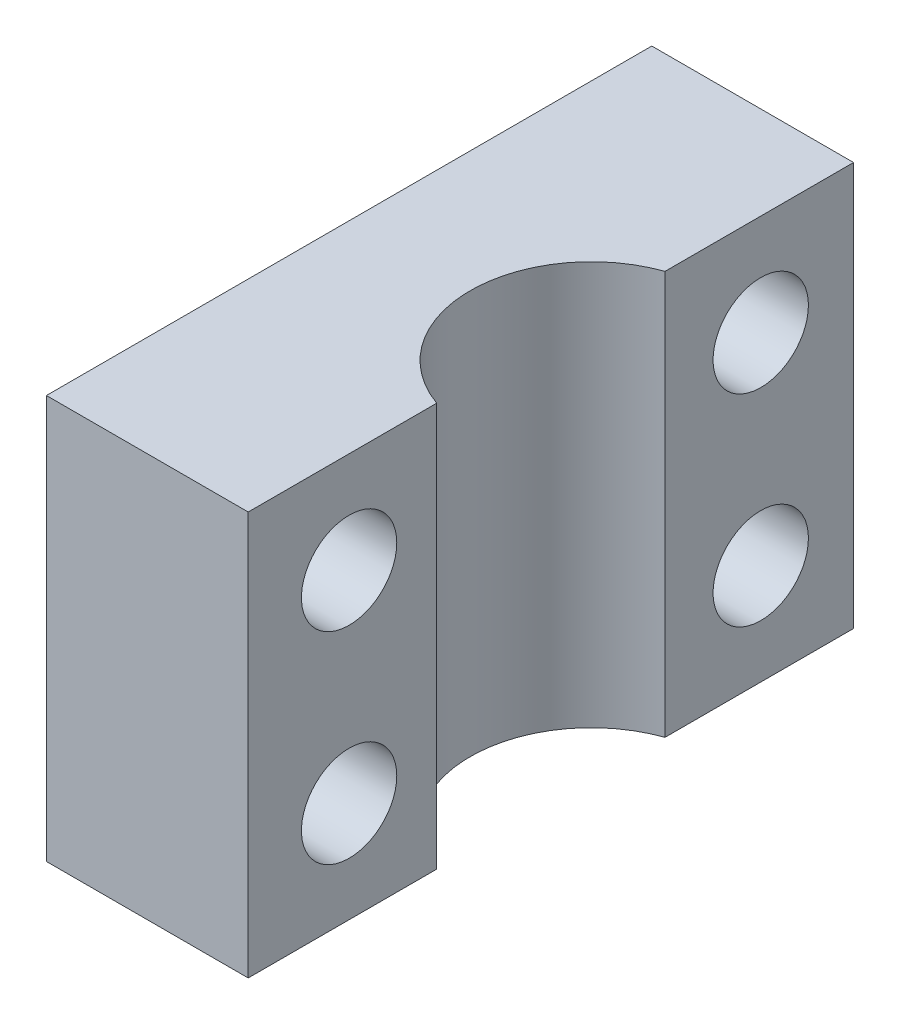
SolidWorks part; units mm, degrees
ref_plane "Front Plane" through (0, 0, 0) normal (0, 0, 1) x (1, 0, 0)
ref_plane "Top Plane" through (0, 0, 0) normal (0, 1, 0) x (1, 0, 0)
ref_plane "Right Plane" through (0, 0, 0) normal (1, 0, 0) x (0, 0, -1)
sketch "Sketch1" plane through (0, 0, 0) normal (0, 1, 0) x (1, 0, 0)
  line L1 (0, 0) -> (12.7, 0)
  line L2 (0, 0) -> (0, 19.05)
  line L3 (0, 19.05) -> (12.7, 19.05)
  line L4 (12.7, 0) -> (12.7, 19.05)
  dimension "D1" = 12.7
  dimension "D2" = 19.05
extrude "Boss-Extrude1" add sketch "Sketch1" along normal blind 12.7
sketch "Sketch4" plane through (0, 12.7, 0) normal (0, 1, 0) x (1, 0, 0)
  line L0 (0, 9.525) -> (6.35, 19.05)
  line L1 (0, 19.05) -> (0, 0) construction
  line L2 (12.7, 19.05) -> (0, 19.05) construction
  line L3 (6.35, 19.05) -> (0, 19.05)
  line L4 (0, 19.05) -> (0, 0)
  line L5 (0, 0) -> (6.35, 0)
  line L6 (0, 0) -> (12.7, 0) construction
  line L7 (6.35, 0) -> (0, 9.525)
  line L8 (12.7, 0) -> (12.7, 19.05) construction
  circle A0 centre (13.97, 9.525) radius 3.81
  point P17 (13.97, 9.525)
  line M1 (0, 19.05) -> (0, 0)
  line M2 (0, 0) -> (12.7, 0)
  line M3 (12.7, 0) -> (12.7, 19.05)
  line M4 (12.7, 19.05) -> (0, 19.05)
  dimension "D1" = 7.62
  dimension "D2" = 1.27
extrude "Cut-Extrude2" cut sketch "Sketch4" against normal blind 12.7 contours L0 M1 M4 | L7 M2 M1 | A0 M3
sketch "Sketch5" plane through (12.7, 0, 0) normal (1, 0, 0) x (0, 0, -1)
  line L0 (0, 12.7) -> (5.9329, 12.7) construction
  line L1 (0, 12.7) -> (0, 0) construction
  circle A0 centre (3.175, 9.525) radius 1.5
  circle A1 centre (16.129, 9.525) radius 1.5
  circle A2 centre (16.129, 3.175) radius 1.5
  circle A3 centre (3.175, 3.175) radius 1.5
  dimension "D1" = 3
  dimension "D2" = 3.175
  dimension "D3" = 3.175
  dimension "D4" = 2
  dimension "D5" = 2
extrude "Cut-Extrude3" cut sketch "Sketch5" against normal blind 12.7
sketch "Sketch6" plane through (0, 0, 0) normal (0, -1, 0) x (1, 0, 0)
  line L0 (6.35, 0) -> (6.35, -5.5703)
  line L2 (2.6365, -5.5703) -> (6.35, 0)
  line L3 (2.6365, -5.5703) -> (6.35, -5.5703)
  line L4 (6.35, 0) -> (0, -9.525) construction
extrude "Cut-Extrude4" cut sketch "Sketch6" against normal blind 12.7
ref_plane "Plane1" through (0, 0, -9.525) normal (0, 0, -1) x (0, 1, 0)
mirror "Mirror1" about plane through (0, 0, -9.525) normal (0, 0, -1) of "Cut-Extrude4"
sketch "Sketch7" plane through (0, 0, 0) normal (0, -1, 0) x (1, 0, 0)
  line L1 (6.35, -13.4797) -> (-5.8631, -13.4797)
  line L2 (6.35, -13.4797) -> (6.35, -3.8712)
  line L3 (6.35, -3.8712) -> (-5.8631, -3.8712)
  line L4 (-5.8631, -13.4797) -> (-5.8631, -3.8712)
extrude "Cut-Extrude5" cut sketch "Sketch7" against normal blind 12.7
